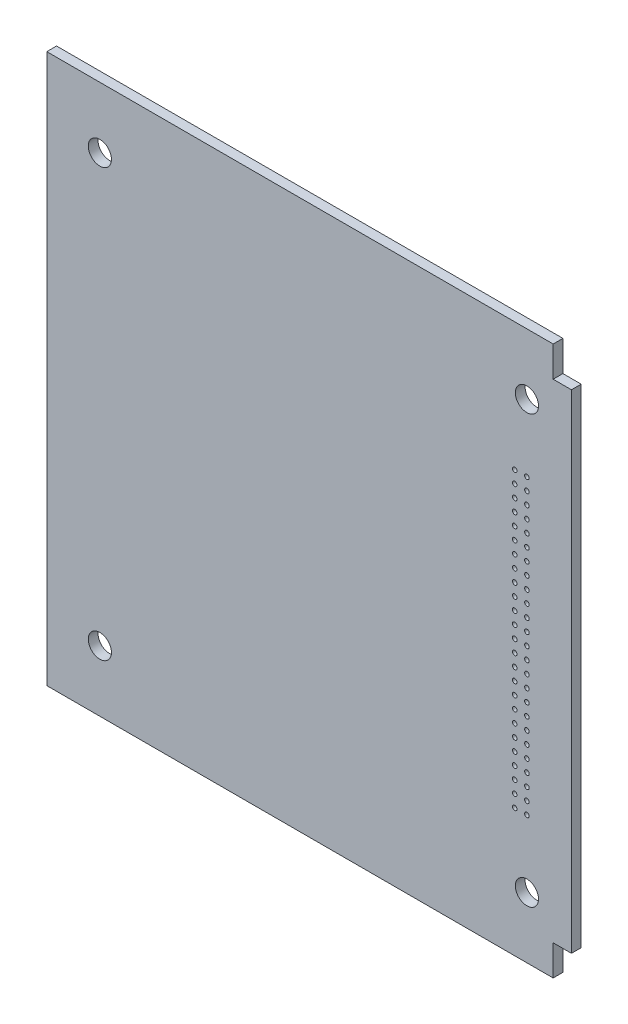
SolidWorks part; units mm, degrees
material "電力回路基板"
ref_plane "正面" through (0, 0, 0) normal (0, 0, 1) x (1, 0, 0)
ref_plane "平面" through (0, 0, 0) normal (0, 1, 0) x (1, 0, 0)
ref_plane "右側面" through (0, 0, 0) normal (1, 0, 0) x (0, 0, -1)
sketch "Sketch1" plane through (0, 0, 0) normal (0, 0, 1) x (1, 0, 0)
  line L0 (-3, 0) -> (-86, 0)
  line L4 (-86, 0) -> (-86, -90)
  line L7 (0, -5) -> (-3, -5)
  line L8 (-3, 0) -> (-3, -5)
  line L11 (0, -85) -> (-3, -85)
  line L12 (-3, -90) -> (-3, -85)
  line L13 (0, -5) -> (0, -85)
  line L14 (-3, -90) -> (-86, -90)
  circle A0 centre (-7.3, -10) radius 1.9
  circle A1 centre (-77.3, -10) radius 1.9
  circle A2 centre (-77.3, -80) radius 1.9
  circle A3 centre (-7.3, -80) radius 1.9
  circle A4 centre (-9.3, -69) radius 0.375
  circle A5 centre (-7.3, -69) radius 0.375
  circle A6 centre (-7.3, -67) radius 0.375
  circle A7 centre (-9.3, -67) radius 0.375
  circle A8 centre (-9.3, -65) radius 0.375
  circle A9 centre (-7.3, -65) radius 0.375
  circle A10 centre (-7.3, -63) radius 0.375
  circle A11 centre (-9.3, -63) radius 0.3838
  circle A12 centre (-9.3, -61) radius 0.375
  circle A13 centre (-7.3, -61) radius 0.375
  circle A14 centre (-7.3, -59) radius 0.375
  circle A15 centre (-9.3, -59) radius 0.375
  circle A16 centre (-7.3, -57) radius 0.375
  circle A17 centre (-9.3, -57) radius 0.375
  circle A18 centre (-9.3, -55) radius 0.375
  circle A19 centre (-7.3, -55) radius 0.375
  circle A20 centre (-7.3, -53) radius 0.375
  circle A21 centre (-9.3, -53) radius 0.375
  circle A22 centre (-9.3, -51) radius 0.375
  circle A23 centre (-7.3, -51) radius 0.375
  circle A24 centre (-7.3, -49) radius 0.375
  circle A25 centre (-9.3, -49) radius 0.375
  circle A26 centre (-9.3, -47) radius 0.375
  circle A27 centre (-7.3, -47) radius 0.375
  circle A28 centre (-7.3, -45) radius 0.375
  circle A29 centre (-9.3, -45) radius 0.3842
  circle A30 centre (-9.3, -43) radius 0.375
  circle A31 centre (-7.3, -43) radius 0.3808
  circle A32 centre (-7.3, -41) radius 0.3774
  circle A33 centre (-9.3, -41) radius 0.3774
  circle A34 centre (-9.3, -39) radius 0.375
  circle A35 centre (-7.3, -39) radius 0.375
  circle A36 centre (-7.3, -37) radius 0.375
  circle A37 centre (-9.3, -37) radius 0.3808
  circle A38 centre (-7.3, -35) radius 0.375
  circle A39 centre (-9.3, -35) radius 0.375
  circle A40 centre (-9.3, -33) radius 0.375
  circle A41 centre (-7.3, -33) radius 0.375
  circle A42 centre (-7.3, -31) radius 0.375
  circle A43 centre (-9.3, -31) radius 0.375
  circle A44 centre (-7.3, -29) radius 0.375
  circle A45 centre (-9.3, -29) radius 0.375
  circle A46 centre (-9.3, -27) radius 0.375
  circle A47 centre (-7.3, -27) radius 0.375
  circle A48 centre (-7.3, -25) radius 0.375
  circle A49 centre (-9.3, -25) radius 0.375
  circle A50 centre (-7.3, -23) radius 0.375
  circle A51 centre (-9.3, -23) radius 0.375
  circle A52 centre (-9.3, -21) radius 0.375
  circle A53 centre (-7.3, -21) radius 0.375
  dimension "D5" = 70
  dimension "D6" = 3
  dimension "D3" = 3.8
  dimension "D10" = 7.3
  dimension "D14" = 10
  dimension "D15" = 10
  dimension "D2" = 90
  dimension "D4" = 70
  dimension "D7" = 5
  dimension "D8" = 86
  dimension "D9" = 7.3
  dimension "D11" = 3
  dimension "D12" = 5
  dimension "D13" = 9.3
  dimension "D16" = 21
extrude "Boss-Extrude1" add sketch "Sketch1" along normal blind 1.6
